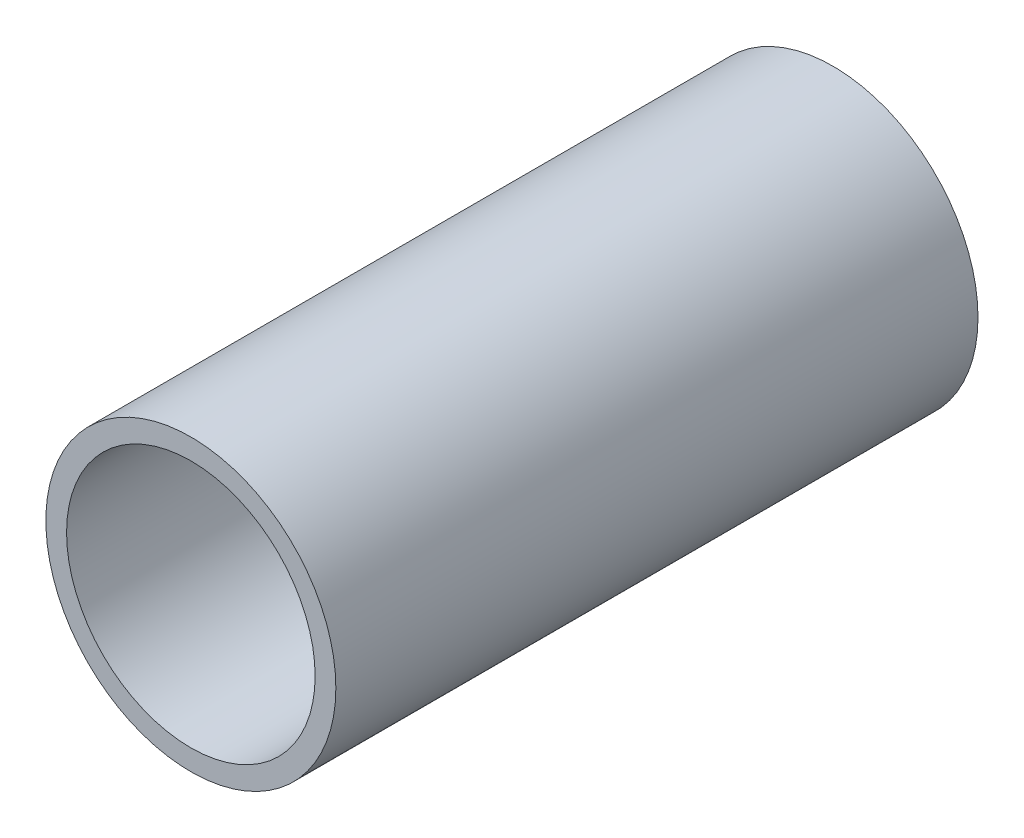
SolidWorks part; units mm, degrees
material "ABS PC"
ref_plane "Front Plane" through (0, 0, 0) normal (0, 0, 1) x (1, 0, 0)
ref_plane "Top Plane" through (0, 0, 0) normal (0, 1, 0) x (1, 0, 0)
ref_plane "Right Plane" through (0, 0, 0) normal (1, 0, 0) x (0, 0, -1)
sketch "Sketch1" plane through (0, 0, 0) normal (0, 0, 1) x (1, 0, 0)
  circle A0 centre (0, 0) radius 44.45
  circle A1 centre (0, 0) radius 38.1
  dimension "D1" = 88.9
  dimension "D2" = 76.2
extrude "Boss-Extrude1" add sketch "Sketch1" along normal mid plane 196.85
